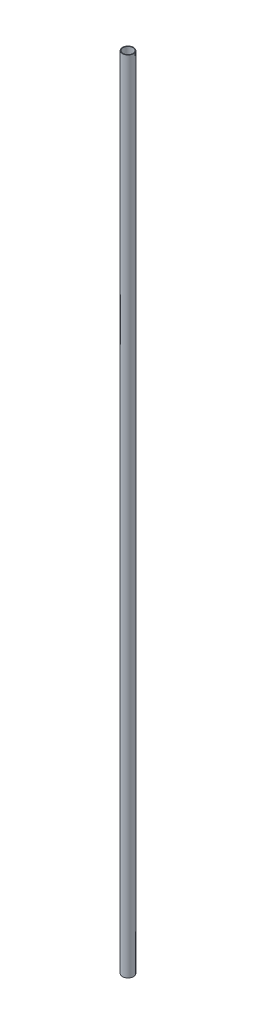
SolidWorks part; units mm, degrees
ref_plane "Front Plane" through (0, 0, 0) normal (0, 0, 1) x (1, 0, 0)
ref_plane "Top Plane" through (0, 0, 0) normal (0, 1, 0) x (1, 0, 0)
ref_plane "Right Plane" through (0, 0, 0) normal (1, 0, 0) x (0, 0, -1)
sketch "Sketch1" plane through (0, 0, 0) normal (0, 1, 0) x (1, 0, 0)
  circle A0 centre (0, 0) radius 13.3223
  circle A1 centre (0, 0) radius 14.7701
  dimension "D1" = 29.5402
  dimension "D2" = 26.6446
extrude "Boss-Extrude1" add sketch "Sketch1" along normal blind 2133.6
